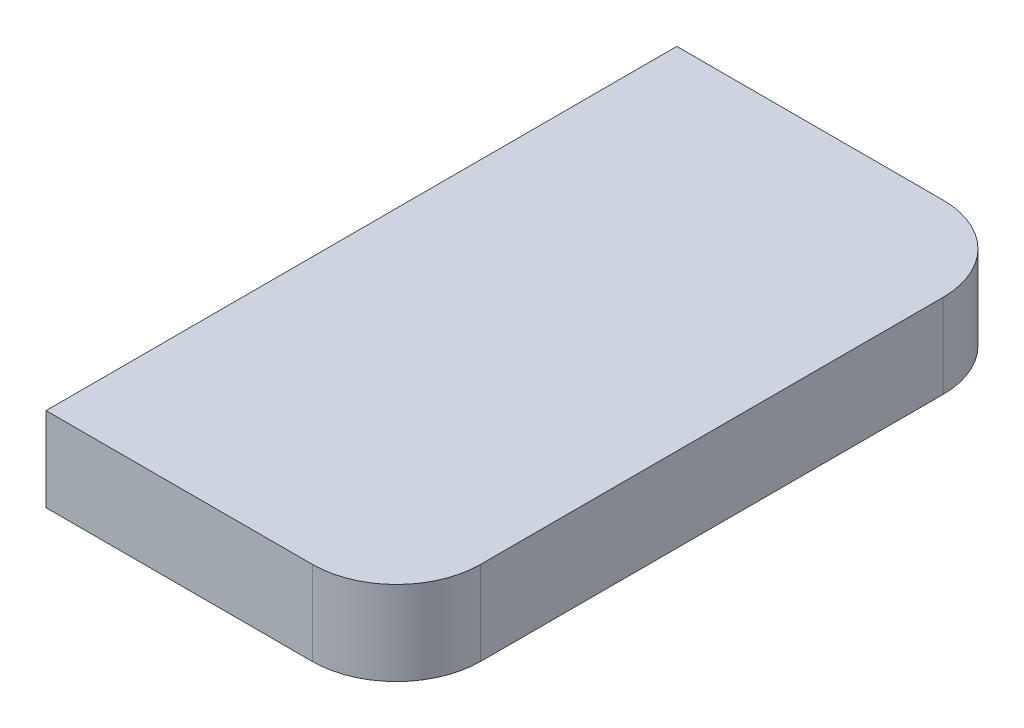
SolidWorks part; units mm, degrees
ref_plane "Front Plane" through (0, 0, 0) normal (0, 0, 1) x (1, 0, 0)
ref_plane "Top Plane" through (0, 0, 0) normal (0, 1, 0) x (1, 0, 0)
ref_plane "Right Plane" through (0, 0, 0) normal (1, 0, 0) x (0, 0, -1)
sketch "Sketch1" plane through (0, 0, 0) normal (0, 1, 0) x (1, 0, 0)
  line L1 (0, 0) -> (100, 0)
  line L2 (0, 0) -> (0, 75)
  line L3 (0, 75) -> (100, 75)
  line L4 (100, 0) -> (100, 75)
  dimension "D1" = 100
  dimension "D2" = 75
extrude "Boss-Extrude1" add sketch "Sketch1" along normal blind 10
fillet "Fillet1" radius 10 4 edges at (0, 5, 0) (0, 5, -75) (100, 5, -75) (100, 5, 0)
sketch "Sketch2" plane through (0, 10, 0) normal (0, 1, 0) x (1, 0, 0)
  line L1 (58.3339, -26.0719) -> (-30.178, -26.0719)
  line L2 (58.3339, -26.0719) -> (58.3339, 103.147)
  line L3 (58.3339, 103.147) -> (-30.178, 103.147)
  line L4 (-30.178, -26.0719) -> (-30.178, 103.147)
extrude "Cut-Extrude1" cut sketch "Sketch2" against normal through all
